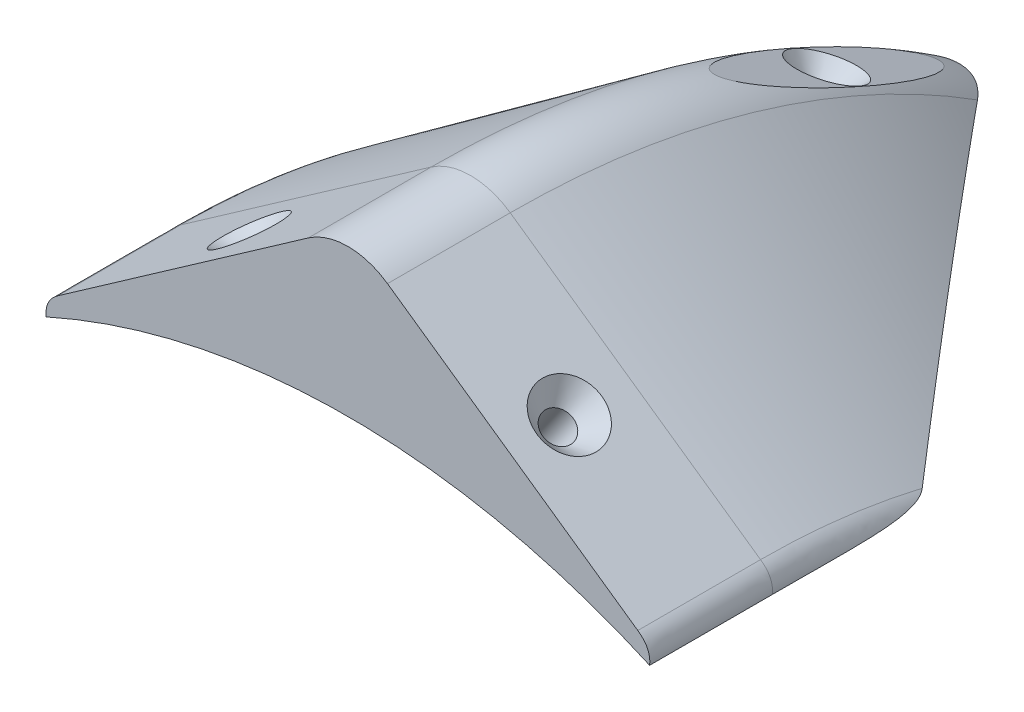
SolidWorks part; units mm, degrees
ref_plane "Front Plane" through (0, 0, 0) normal (0, 0, 1) x (1, 0, 0)
ref_plane "Top Plane" through (0, 0, 0) normal (0, 1, 0) x (1, 0, 0)
ref_plane "Right Plane" through (0, 0, 0) normal (1, 0, 0) x (0, 0, -1)
sketch "Sketch1" plane through (0, 0, 0) normal (0, 0, 1) x (1, 0, 0)
  line L0 (0, 0) -> (0, 152.4) construction
  line L1 (-59.9912, 144.0357) -> (-8.1938, 180.2969)
  line L7 (0, 0) -> (74.48, 0) construction
  line L20 (59.9912, 144.0357) -> (8.1938, 180.2969)
  arc A1 (8.1938, 180.2969) -> (-8.1938, 180.2969) centre (0, 168.5925) ccw
  arc A7 (62.4412, 139.0211) -> (-62.4412, 139.0211) centre (0, 0) ccw
  spline S2 degree 2 poles (-59.9912, 144.0357) (-62.7825, 142.084) (-62.4412, 139.0211) knots 0 0 0 1 1 1
  spline S3 degree 2 poles (59.9912, 144.0357) (62.7825, 142.084) (62.4412, 139.0211) knots 0 0 0 1 1 1
  dimension "D2" = 63.2286
  dimension "D3" = 28.575
  dimension "D12" = 5.8922
  dimension "D5" = 152.4
  dimension "D1" = 168.5925
  dimension "D4" = 51.7974
  dimension "D14" = 1.791
  dimension "D15" = 3.2237
revolve "Revolve1" add sketch "Sketch1" angle 57 about L7
sketch "Sketch3" plane through (0, 0, 0) normal (0, 0, 1) x (1, 0, 0)
  line L0 (0, 0) -> (0, 152.4) construction
  line L2 (-59.9912, 144.0357) -> (-8.1938, 180.2969)
  line L4 (19.2885, 0) -> (93.7685, 0) construction
  line L5 (59.9912, 144.0357) -> (8.1938, 180.2969)
  arc A2 (8.1938, 180.2969) -> (-8.1938, 180.2969) centre (0, 168.5925) ccw
  arc A3 (62.4412, 139.0211) -> (-62.4412, 139.0211) centre (0, 0) ccw
  spline S0 degree 2 poles (-59.9912, 144.0357) (-62.7825, 142.084) (-62.4412, 139.0211) knots 0 0 0 1 1 1
  spline S1 degree 2 poles (59.9912, 144.0357) (62.7825, 142.084) (62.4412, 139.0211) knots 0 0 0 1 1 1
  dimension "D2" = 28.575
  dimension "D3" = 5.8922
  dimension "D8" = 152.4
  dimension "D1" = 168.5925
  dimension "D4" = 1.791
  dimension "D5" = 3.2237
  dimension "D6" = 63.2286
  dimension "D7" = 51.7974
extrude "Boss-Extrude1" add sketch "Sketch3" along normal blind 25.4
ref_plane "Plane1" through (0, 0, 12.7) normal (0, 0, 1) x (1, 0, 0)
sketch "Sketch7" plane through (0, 0, 12.7) normal (0, 0, 1) x (1, 0, 0)
  line L0 (-30.5085, 164.6753) -> (-18.8551, 148.029) construction
  line L1 (-8.1938, 180.2969) -> (-59.9912, 144.0357) construction
  line L2 (-18.8551, 148.029) -> (-21.4561, 146.2082)
  line L3 (-21.4561, 146.2082) -> (-37.8066, 169.5641) construction
  line L4 (-30.7642, 159.5044) -> (-19.1086, 167.6641) construction
  line L5 (-21.4561, 146.2082) -> (-33.1095, 162.8545)
  line L6 (-18.8551, 148.029) -> (-28.1633, 161.3253)
  line L7 (-33.1095, 162.8545) -> (-27.585, 166.722)
  line L8 (-27.585, 166.722) -> (-28.1633, 161.3253)
  line L9 (0, 0) -> (0, 246.8513) construction
  circle A0 centre (0, 0) radius 152.4 construction
  circle A1 centre (0, 0) radius 149.225 construction
  dimension "D1" = 16.2306
  dimension "D2" = 3.175
  dimension "D3" = 4.0894
  dimension "D4" = 6.7437
revolve "Cut-Revolve2" cut sketch "Sketch7" angle 360 about L3
mirror "Mirror2" about plane through (0, 0, 0) normal (1, 0, 0) of "Cut-Revolve2"
sketch "Sketch8" plane through (0, 0, 25.4) normal (0, 0, 1) x (1, 0, 0)
  circle A0 centre (0, 0) radius 152.4
extrude "Cut-Extrude3" cut sketch "Sketch8" against normal blind 257.048
sketch "Sketch10" plane through (0, 0, 0) normal (1, 0, 0) x (0, 0, -1)
  line L0 (0, 0) -> (74.384, 167.0692)
  line L1 (0, 0) -> (0, 180.2969) construction
  line L2 (0, 0) -> (50.4086, 175.7955)
  line L3 (50.4086, 175.7955) -> (74.384, 167.0692)
  arc A1 (101.0907, 152.4) -> (0, 182.88) centre (0, 0) ccw construction
  dimension "D1" = 24
  dimension "D2" = 16
  dimension "D3" = 25.5141
ref_plane "Plane2" through (0, 167.0692, -74.384) normal (0, 0.9135, -0.4067) x (1, 0, 0)
sketch "Sketch13" plane through (0, 167.0692, -74.384) normal (0, 0.9135, -0.4067) x (1, 0, 0)
  line L0 (8.1938, 26.4309) -> (8.1938, -73.3334) construction
  line L1 (8.1938, 63.5) -> (-8.1938, 63.5)
  line L2 (8.1938, 63.5) -> (8.1938, -63.5)
  line L3 (8.1938, -63.5) -> (-8.1938, -63.5)
  line L4 (-8.1938, 63.5) -> (-8.1938, -63.5)
  line L5 (-8.1938, 26.4309) -> (-8.1938, -73.3334) construction
  dimension "D1" = 127
  dimension "D2" = 63.5
extrude "Cut-Extrude5" cut sketch "Sketch13" against normal blind 1.778
sketch "Sketch14" plane through (0, 0, 0) normal (1, 0, 0) x (0, 0, -1)
  line L0 (73.6608, 165.4449) -> (67.5001, 168.1878)
  line L1 (96.9008, 155.0978) -> (50.4208, 175.792) construction
  line L2 (73.6608, 165.4449) -> (63.3297, 142.2409)
  line L3 (0, 0) -> (74.384, 167.0692) construction
  line L4 (63.3297, 142.2409) -> (60.4292, 143.5322)
  line L5 (60.4292, 143.5322) -> (69.097, 163.0004)
  line L6 (67.5001, 168.1878) -> (69.097, 163.0004)
  dimension "D1" = 6.7437
  dimension "D2" = 25.4
  dimension "D3" = 3.175
  dimension "D4" = 21.3106
revolve "Cut-Revolve4" cut sketch "Sketch14" angle 360 about L2
sketch "Sketch15" plane through (0, 167.0692, -74.384) normal (0, 0.9135, -0.4067) x (1, 0, 0)
  circle A0 centre (0, 0) radius 19.7251
